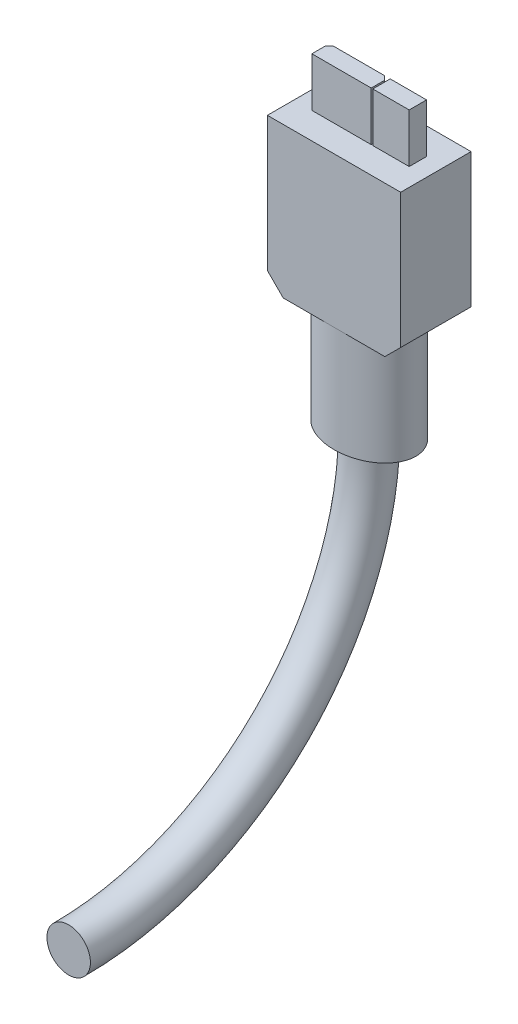
SolidWorks part; units mm, degrees
ref_plane "Front Plane" through (0, 0, 0) normal (0, 0, 1) x (1, 0, 0)
ref_plane "Top Plane" through (0, 0, 0) normal (0, 1, 0) x (1, 0, 0)
ref_plane "Right Plane" through (0, 0, 0) normal (1, 0, 0) x (0, 0, -1)
sketch "Sketch1" plane through (0, 0, 0) normal (0, 1, 0) x (1, 0, 0)
  line L1 (0, 0) -> (16.85, 0)
  line L2 (0, 0) -> (0, 8.9)
  line L3 (0, 8.9) -> (16.85, 8.9)
  line L4 (16.85, 0) -> (16.85, 8.9)
  dimension "D1" = 8.9
  dimension "D2" = 16.85
extrude "Boss-Extrude1" add sketch "Sketch1" along normal blind 19
sketch "Sketch2" plane through (0, 19, 0) normal (0, 1, 0) x (1, 0, 0)
  line L0 (0, 4.45) -> (16.85, 4.45) construction
  line L1 (0, 8.9) -> (0, 0) construction
  line L2 (16.85, 0) -> (16.85, 8.9) construction
  line L3 (8.425, 8.9) -> (8.425, 0) construction
  line L4 (16.85, 8.9) -> (0, 8.9) construction
  line L5 (0, 0) -> (16.85, 0) construction
  line L6 (9.775, 5.55) -> (9.775, 3.35)
  line L7 (2.275, 5.55) -> (9.775, 5.55)
  line L8 (2.275, 5.55) -> (2.275, 3.35)
  line L9 (2.275, 3.35) -> (9.775, 3.35)
  line L14 (14.575, 5.55) -> (14.575, 3.35)
  line L15 (14.575, 5.55) -> (9.975, 5.55)
  line L16 (14.575, 3.35) -> (9.975, 3.35)
  line L17 (9.975, 3.35) -> (9.975, 5.55)
  dimension "D1" = 2.2
  dimension "D2" = 1.1
  dimension "D3" = 12.3
  dimension "D4" = 6.15
  dimension "D5" = 7.5
  dimension "D6" = 0.2
extrude "Boss-Extrude2" add sketch "Sketch2" along normal blind 6.2
chamfer "Chamfer1" distance 0.5 angle 45 2 edges at (9.775, 22.1, -5.55) (2.275, 22.1, -5.55)
sketch "Sketch3" plane through (0, 0, 0) normal (0, -1, 0) x (1, 0, 0)
  line L0 (0, 0) -> (16.85, 0) construction
  line L1 (16.85, -8.9) -> (0, -8.9) construction
  line L2 (8.425, 0) -> (8.425, -8.9) construction
  ellipse E0 centre (8.425, -4.45) end of major axis (2.525, -4.45) minor radius 4.45
  point P1 (8.425, -4.45)
  point P9 (0, 0)
  point P14 (0, 0)
  point P15 (0, 0)
  point P16 (0, 0)
  point P17 (8.425, 0)
  dimension "D1" = 11.8
extrude "Boss-Extrude3" add sketch "Sketch3" along normal blind 13.4
chamfer "Chamfer2" distance 2 angle 45 2 edges at (16.85, 0, -4.45) (0, 0, -4.45)
sketch "Sketch4" plane through (0, -13.4, 0) normal (0, -1, 0) x (1, 0, 0)
  line L0 (8.425, 0) -> (8.425, -8.9) construction
  circle A0 centre (8.425, -4.45) radius 2.75
  ellipse E0 centre (8.425, -4.45) end of major axis (2.525, -4.45) minor radius 4.45 construction
  point P11 (0, 0)
  dimension "D1" = 5.5
sketch "Sketch6" plane through (0, 0, 0) normal (1, 0, 0) x (0, 0, -1)
  arc A0 (4.45, -13.4) -> (-33.55, -51.4) centre (-33.55, -13.4) cw
  point P3 (0, 0)
  point P4 (0, 0)
  point P5 (0, 0)
  dimension "D1" = 38
sweep "Sweep2" add profiles "Sketch4" path "Sketch6"
